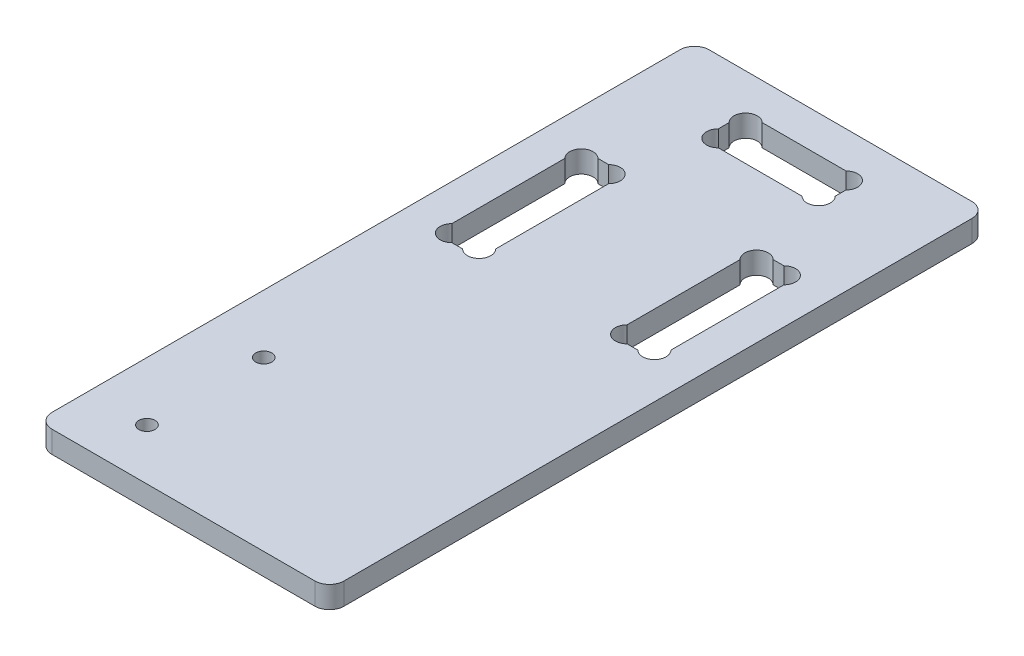
SolidWorks part; units mm, degrees
ref_plane "Plan de face" through (0, 0, 0) normal (0, 0, 1) x (1, 0, 0)
ref_plane "Plan de dessus" through (0, 0, 0) normal (0, 1, 0) x (1, 0, 0)
ref_plane "Plan de droite" through (0, 0, 0) normal (1, 0, 0) x (0, 0, -1)
sketch "Esquisse1" plane through (0, 0, 0) normal (0, 1, 0) x (1, 0, 0)
  line L5 (13, 2) -> (13, 88)
  line L7 (15, 0) -> (51, 0)
  line L8 (53, 88) -> (53, 2)
  line L11 (15, 90) -> (51, 90)
  arc A0 (51, 90) -> (53, 88) centre (51, 88) cw
  arc A1 (15, 0) -> (13, 2) centre (15, 2) cw
  arc A2 (51, 0) -> (53, 2) centre (51, 2) ccw
  arc A3 (15, 90) -> (13, 88) centre (15, 88) ccw
  point P12 (53, 90)
  point P15 (13, 0)
  point P26 (13, 90)
  dimension "D3" = 2
  dimension "D5" = 2
  dimension "D1" = 90
  dimension "D2" = 40
  dimension "D4" = 13
extrude "Extrusion1" add sketch "Esquisse1" along normal blind 3
sketch "Esquisse2" plane through (0, 0, 0) normal (0, -1, 0) x (1, 0, 0)
  line L0 (13, -88) -> (13, -2) construction
  line L1 (15, 0) -> (51, 0) construction
  line L2 (51, -90) -> (15, -90) construction
  line L16 (41, -82.7373) -> (41, -81.2627)
  line L18 (45.7373, -49.5) -> (44.2627, -49.5)
  line L19 (45.7373, -69.5) -> (44.2627, -69.5)
  line L20 (25, -82.7373) -> (25, -81.2627)
  line L21 (38.7373, -85) -> (27.2627, -85)
  line L22 (38.7373, -79) -> (27.2627, -79)
  line L23 (48, -67.2373) -> (48, -51.7627)
  line L24 (42, -67.2373) -> (42, -51.7627)
  line L25 (24, -67.2373) -> (24, -51.7627)
  line L26 (18, -67.2373) -> (18, -51.7627)
  line L27 (20.2627, -69.5) -> (21.7373, -69.5)
  line L28 (20.2627, -49.5) -> (21.7373, -49.5)
  arc A0 (44.2627, -49.5) -> (42, -51.7627) centre (43.1314, -50.6314) ccw
  arc A1 (38.7373, -85) -> (41, -82.7373) centre (39.8686, -83.8686) ccw
  arc A2 (38.7373, -79) -> (41, -81.2627) centre (39.8686, -80.1314) cw
  arc A3 (27.2627, -85) -> (25, -82.7373) centre (26.1314, -83.8686) cw
  arc A4 (27.2627, -79) -> (25, -81.2627) centre (26.1314, -80.1314) ccw
  arc A5 (45.7373, -49.5) -> (48, -51.7627) centre (46.8686, -50.6314) cw
  arc A6 (44.2627, -69.5) -> (42, -67.2373) centre (43.1314, -68.3686) cw
  arc A7 (45.7373, -69.5) -> (48, -67.2373) centre (46.8686, -68.3686) ccw
  arc A8 (20.2627, -69.5) -> (18, -67.2373) centre (19.1314, -68.3686) cw
  arc A9 (21.7373, -69.5) -> (24, -67.2373) centre (22.8686, -68.3686) ccw
  arc A10 (20.2627, -49.5) -> (18, -51.7627) centre (19.1314, -50.6314) ccw
  arc A11 (21.7373, -49.5) -> (24, -51.7627) centre (22.8686, -50.6314) cw
  circle A14 centre (21, -7) radius 1.1
  circle A15 centre (21, -23) radius 1.1
  point P4 (0, 0)
  point P5 (0, 0)
  point P8 (0, 0)
  point P9 (0, 0)
  point P10 (0, 0)
  point P11 (0, 0)
  point P12 (0, 0)
  point P13 (0, 0)
  dimension "D15" = 1
  dimension "D17" = 1.6
  dimension "D4" = 2.2
  dimension "D5" = 2.2
  dimension "D1" = 8
  dimension "D2" = 16
  dimension "D3" = 7
  dimension "D6" = 6
  dimension "D7" = 16
  dimension "D8" = 6
  dimension "D9" = 20
  dimension "D10" = 6
  dimension "D11" = 20
  dimension "D12" = 5
  dimension "D13" = 12
  dimension "D14" = 9.5
  dimension "D16" = 18
  dimension "D18" = 1.1314
  dimension "D19" = 2.2627
  dimension "D20" = 1.1314
  dimension "D21" = 2.2627
  dimension "D22" = 1.1314
  dimension "D23" = 1.1314
  dimension "D24" = 1.1314
  dimension "D25" = 2.2627
  dimension "D26" = 1.1314
  dimension "D27" = 1.1314
  dimension "D28" = 1.1314
  dimension "D29" = 1.1314
  dimension "D30" = 2.2627
  dimension "D31" = 1.1314
  dimension "D32" = 1.1314
  dimension "D33" = 1.1314
extrude "Enlèv. mat.-Extru.1" cut sketch "Esquisse2" against normal through all
